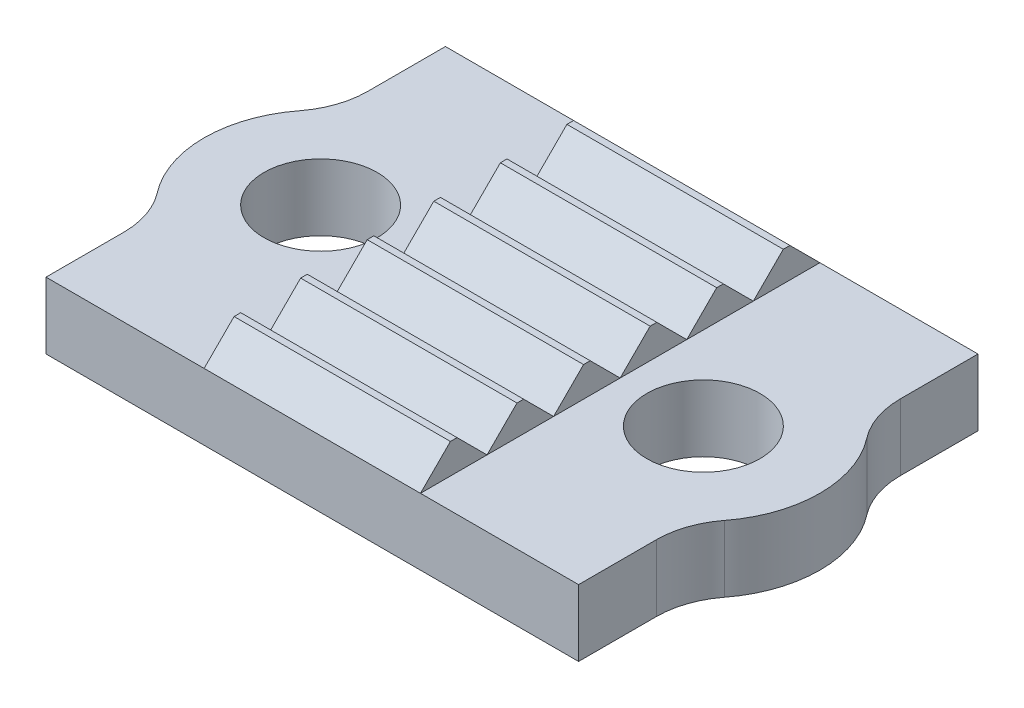
SolidWorks part; units mm, degrees
ref_plane "Alzado" through (0, 0, 0) normal (0, 0, 1) x (1, 0, 0)
ref_plane "Planta" through (0, 0, 0) normal (0, 1, 0) x (1, 0, 0)
ref_plane "Vista lateral" through (0, 0, 0) normal (1, 0, 0) x (0, 0, -1)
sketch "Croquis1" plane through (0, 0, 0) normal (0, 1, 0) x (1, 0, 0)
  line L0 (0, -16.4018) -> (0, 78.9163) construction
  line L1 (-63.9099, 0) -> (63.9099, 0) construction
  line L2 (-8, 6) -> (8, 6)
  line L3 (8, 6) -> (8, 3.6657)
  line L4 (-8, -6) -> (8, -6)
  line L5 (8, -6) -> (8, -3.6657)
  line L6 (-8, -6) -> (-8, -3.6657)
  line L7 (-8, 6) -> (-8, 3.6657)
  circle A0 centre (5.75, 0) radius 1.7
  arc A1 (8.5208, -2.1383) -> (8.5208, 2.1383) centre (5.75, 0) ccw
  arc A2 (8, 3.6657) -> (8.5208, 2.1383) centre (10.5, 3.6657) ccw
  arc A3 (8, -3.6657) -> (8.5208, -2.1383) centre (10.5, -3.6657) cw
  arc A4 (-8, -3.6657) -> (-8.5208, -2.1383) centre (-10.5, -3.6657) ccw
  arc A5 (-8, 3.6657) -> (-8.5208, 2.1383) centre (-10.5, 3.6657) cw
  arc A6 (-8.5208, -2.1383) -> (-8.5208, 2.1383) centre (-5.75, 0) cw
  circle A7 centre (-5.75, 0) radius 1.7
  point P10 (8, 0)
  point P19 (0, 0)
  point P28 (0, -6)
  point P29 (-8, 0)
  point P30 (0, 6)
  dimension "D1" = 3.4
  dimension "D5" = 7
  dimension "D6" = 5
  dimension "D2" = 5.75
  dimension "D3" = 8
  dimension "D4" = 6
extrude "Saliente-Extruir1" add sketch "Croquis1" along normal blind 2
ref_plane "Plano1" through (3.25, 0, 0) normal (1, 0, 0) x (0, 0, -1)
sketch "Croquis3" plane through (0, 2, 0) normal (0, 1, 0) x (1, 0, 0)
  line L0 (3.5, -6) -> (3.5, 6) construction
  line L1 (-8, -6) -> (8, -6) construction
  line L2 (8, 6) -> (-8, 6) construction
  point P6 (0, -6)
  dimension "D1" = 3.5
sketch "Croquis4" plane through (3.25, 0, 0) normal (1, 0, 0) x (0, 0, -1)
  line L0 (-6, 2) -> (-4, 2)
  line L1 (-6, 2) -> (-5.1, 2.9)
  line L2 (-5, 3) -> (-5, 2) construction
  line L3 (-4, 2) -> (-4.9, 2.9)
  line L4 (-5.1, 2.9) -> (-4.9, 2.9)
  dimension "D1" = 1
  dimension "D2" = 1
  dimension "D3" = 0.9
extrude "Saliente-Extruir2" add sketch "Croquis4" against normal blind 6.5
pattern_linear "MatrizL1" count 6 spacing 2 along (0, 0, -1) of "Saliente-Extruir2"
